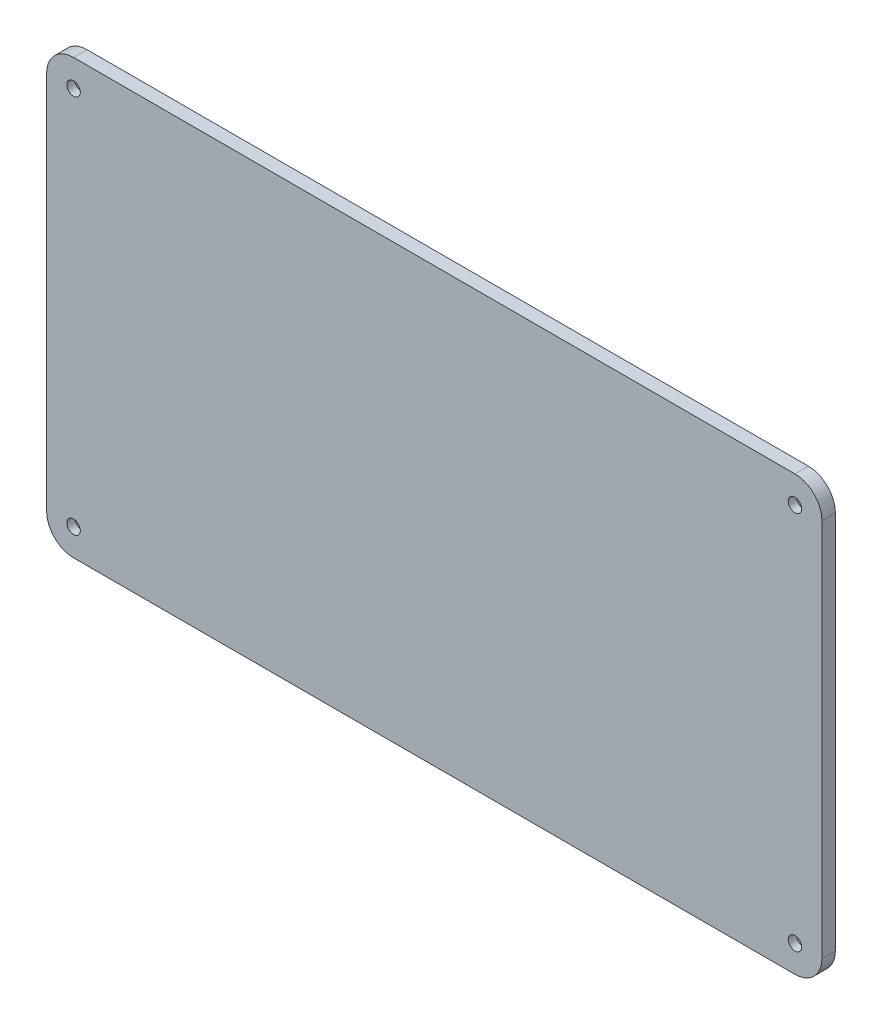
SolidWorks part; units mm, degrees
material "ABS"
ref_plane "Front Plane" through (0, 0, 0) normal (0, 0, 1) x (1, 0, 0)
ref_plane "Top Plane" through (0, 0, 0) normal (0, 1, 0) x (1, 0, 0)
ref_plane "Right Plane" through (0, 0, 0) normal (1, 0, 0) x (0, 0, -1)
sketch "Sketch1" plane through (0, 0, 0) normal (0, 0, 1) x (1, 0, 0)
  line L1 (10, 0) -> (278, 0)
  line L2 (0, 10) -> (0, 151)
  line L3 (10, 161) -> (278, 161)
  line L4 (288, 10) -> (288, 151)
  arc A0 (278, 161) -> (288, 151) centre (278, 151) cw
  arc A1 (278, 0) -> (288, 10) centre (278, 10) ccw
  arc A2 (10, 0) -> (0, 10) centre (10, 10) cw
  arc A3 (0, 151) -> (10, 161) centre (10, 151) cw
  point P11 (0, 0)
  dimension "D3" = 10
  dimension "D1" = 288
  dimension "D2" = 161
extrude "Boss-Extrude1" add sketch "Sketch1" along normal blind 5
sketch "Sketch2" plane through (0, 0, 5) normal (0, 0, 1) x (1, 0, 0)
  line L0 (0, 151) -> (0, 10) construction
  line L1 (278, 161) -> (10, 161) construction
  circle A0 centre (10, 151) radius 0.8
  circle A1 centre (278, 151) radius 0.8
  circle A2 centre (10, 10) radius 0.8
  circle A3 centre (278, 10) radius 0.8
  arc A5 (288, 151) -> (278, 161) centre (278, 151) ccw construction
  arc A6 (278, 0) -> (288, 10) centre (278, 10) ccw construction
  arc A7 (0, 10) -> (10, 0) centre (10, 10) ccw construction
  dimension "D1" = 1.6
  dimension "D3" = 10
  dimension "D2" = 10
extrude "Cut-Extrude1" cut sketch "Sketch2" against normal through all
sketch "Sketch3" plane through (0, 0, 5) normal (0, 0, 1) x (1, 0, 0)
  circle A0 centre (10, 151) radius 2.5
  circle A1 centre (10, 151) radius 0.8 construction
  circle A2 centre (10, 10) radius 2.5
  circle A4 centre (278, 10) radius 2.5
  circle A5 centre (278, 151) radius 2.5
  circle A7 centre (10, 10) radius 0.8 construction
  circle A8 centre (278, 10) radius 0.8 construction
  circle A9 centre (278, 151) radius 0.8 construction
  dimension "D1" = 5
extrude "Cut-Extrude2" cut sketch "Sketch3" against normal blind 3
